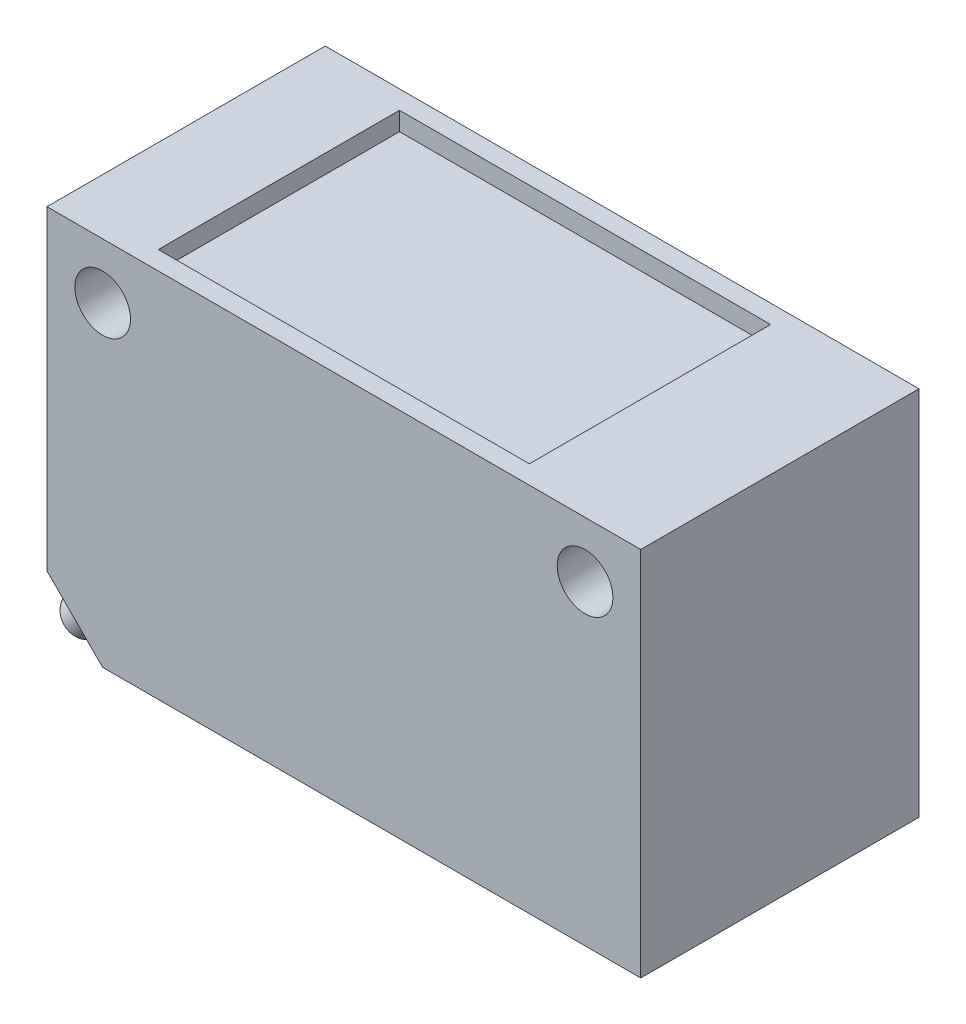
SolidWorks part; units mm, degrees
ref_plane "Plan de face" through (0, 0, 0) normal (0, 0, 1) x (1, 0, 0)
ref_plane "Plan de dessus" through (0, 0, 0) normal (0, 1, 0) x (1, 0, 0)
ref_plane "Plan de droite" through (0, 0, 0) normal (1, 0, 0) x (0, 0, -1)
sketch "Esquisse2" plane through (0, 0, 0) normal (0, 0, 1) x (1, 0, 0)
  line L1 (-16, 10) -> (16, 10)
  line L2 (-16, 10) -> (-16, -10)
  line L3 (-16, -10) -> (16, -10)
  line L4 (16, 10) -> (16, -10)
  dimension "D1" = 32
  dimension "D2" = 20
  dimension "D3" = 16
  dimension "D4" = 10
extrude "Boss.-Extru.1" add sketch "Esquisse2" along normal blind 15
sketch "Esquisse3" plane through (0, 0, 15) normal (0, 0, 1) x (1, 0, 0)
  line L0 (16, 10) -> (-16, 10) construction
  line L1 (-16, 10) -> (-16, -10) construction
  circle A0 centre (-13, 7) radius 1.5
  dimension "D1" = 3
  dimension "D2" = 3
  dimension "D3" = 3
extrude "Enlèv. mat.-Extru.1" cut sketch "Esquisse3" against normal blind 15
mirror "Symétrie1" about plane through (0, 0, 0) normal (1, 0, 0) of "Enlèv. mat.-Extru.1"
chamfer "Chanfrein1" distance 3 angle 45 1 edges at (-16, -10, 7.5)
sketch "Esquisse5" plane through (-11.5, -11.5, 0) normal (-0.7071, -0.7071, 0) x (0, 0, 1)
  line L0 (15, 2.1213) -> (0, 2.1213) construction
  line L3 (15, 6.364) -> (15, 2.1213) construction
  circle A0 centre (7.5, 4.2413) radius 1
  dimension "D1" = 2
  dimension "D2" = 2.12
  dimension "D3" = 7.5
extrude "Boss.-Extru.2" add sketch "Esquisse5" along normal blind 10
sketch "Esquisse6" plane through (0, 10, 0) normal (0, 1, 0) x (1, 0, 0)
  line L0 (16, 0) -> (-16, 0) construction
  line L1 (9, -14) -> (-11, -14)
  line L2 (9, -14) -> (9, -1)
  line L3 (9, -1) -> (-11, -1)
  line L4 (-11, -14) -> (-11, -1)
  line L5 (-16, -15) -> (-16, 0) construction
  line L6 (16, -15) -> (16, 0) construction
  dimension "D1" = 13
  dimension "D2" = 1
  dimension "D3" = 5
  dimension "D4" = 7
extrude "Enlèv. mat.-Extru.2" cut sketch "Esquisse6" against normal blind 1
